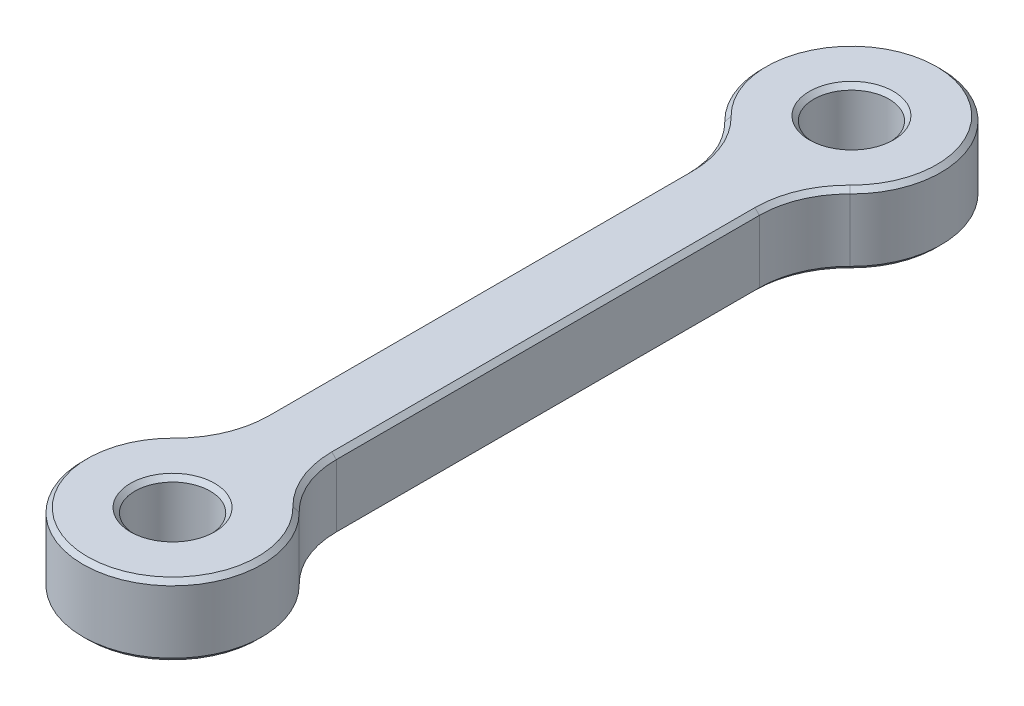
SolidWorks part; units mm, degrees
ref_plane "Front Plane" through (0, 0, 0) normal (0, 0, 1) x (1, 0, 0)
ref_plane "Top Plane" through (0, 0, 0) normal (0, 1, 0) x (1, 0, 0)
ref_plane "Right Plane" through (0, 0, 0) normal (1, 0, 0) x (0, 0, -1)
sketch "Sketch1" plane through (0, 0, 0) normal (0, 1, 0) x (1, 0, 0)
  line L0 (0, 37.9) -> (0, -37.9) construction
  line L1 (-4, 28.7348) -> (-4, -28.7348)
  line L2 (4, -28.7348) -> (4, 28.7348)
  circle A0 centre (0, 37.9) radius 4.2
  circle A1 centre (0, -37.9) radius 4.2
  arc A2 (4, 28.7348) -> (-4, 28.7348) centre (0, 37.9) ccw
  arc A3 (-4, -28.7348) -> (4, -28.7348) centre (0, -37.9) ccw
  dimension "D2" = 8.4
  dimension "D3" = 20
  dimension "D1" = 75.8
  dimension "D4" = 8
extrude "Boss-Extrude1" add sketch "Sketch1" along normal blind 8
fillet "Fillet1" radius 10 4 edges at (4, 4, 28.7348) (4, 4, -28.7348) (-4, 4, -28.7348) (-4, 4, 28.7348)
chamfer "Chamfer1" distance 0.5 angle 45 20 edges at (0, 0, 42.1) (0, 0, -33.7) (-4.7805, 0, -27.4901) (-4, 0, 0) (-4.7805, 0, 27.4901) (0, 0, 47.9) (4.7805, 0, 27.4901) (4, 0, 0) (4.7805, 0, -27.4901) (0, 0, -47.9) (0, 8, 42.1) (4.7805, 8, 27.4901) (0, 8, 47.9) (-4.7805, 8, 27.4901) (-4, 8, 0) (-4.7805, 8, -27.4901) (0, 8, -47.9) (4.7805, 8, -27.4901) (4, 8, 0) (0, 8, -33.7)
